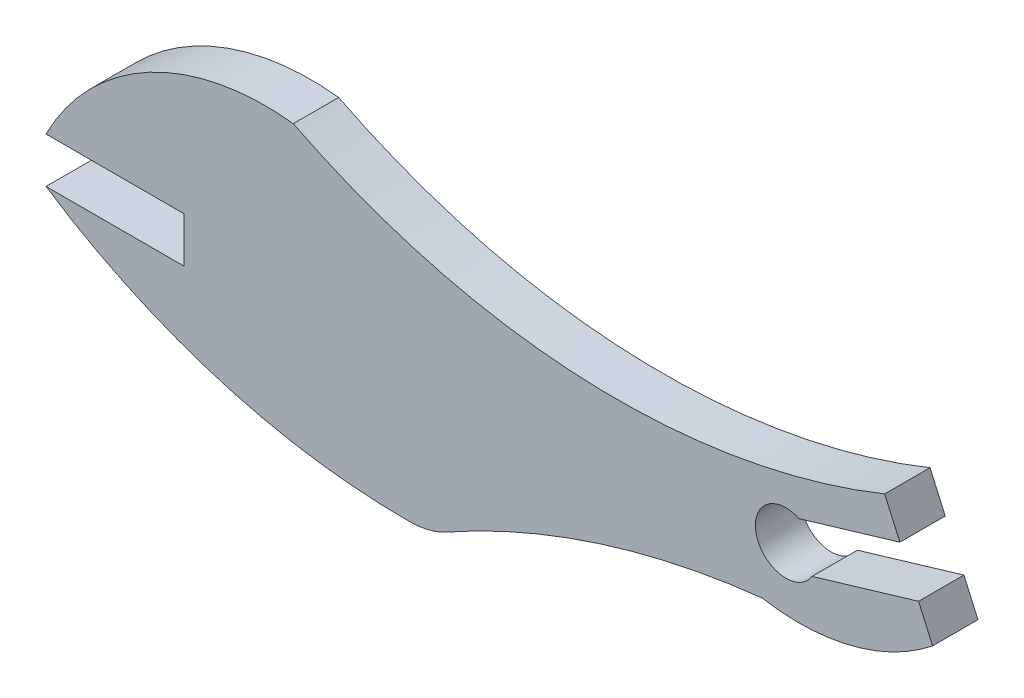
SolidWorks part; units mm, degrees
ref_plane "Front Plane" through (0, 0, 0) normal (0, 0, 1) x (1, 0, 0)
ref_plane "Top Plane" through (0, 0, 0) normal (0, 1, 0) x (1, 0, 0)
ref_plane "Right Plane" through (0, 0, 0) normal (1, 0, 0) x (0, 0, -1)
sketch "Sketch1" plane through (0, 0, 0) normal (0, 0, 1) x (1, 0, 0)
  line L0 (4.3603, 0) -> (4.3603, -1.524)
  line L1 (4.3603, -1.524) -> (-0.27, -1.524)
  line L2 (29.5018, 0) -> (29.0286, 1.062)
  line L3 (4.3603, 0) -> (-0.27, 0)
  line L4 (28.403, 2.4658) -> (27.8911, 3.6146)
  line L5 (28.403, 2.4658) -> (25.0182, 1.4583)
  line L6 (29.0286, 1.062) -> (25.453, -0.0024)
  arc A0 (-0.27, -1.524) -> (11.9642, -5.1656) centre (11.871, 16.8934) ccw
  arc A1 (13.1933, -4.8424) -> (23.7736, -1.4699) centre (26.7445, -29.0729) cw
  arc A2 (11.9642, -5.1656) -> (13.1933, -4.8424) centre (11.9534, -2.6256) ccw
  arc A3 (27.8911, 3.6146) -> (8.0338, 4.4536) centre (18.8892, 25.9668) cw
  arc A4 (-0.27, 0) -> (8.0338, 4.4536) centre (7.0928, -3.7601) cw
  arc A5 (29.5018, 0) -> (23.7736, -1.4699) centre (25.0066, 5.6214) cw
  arc A6 (25.0182, 1.4583) -> (25.453, -0.0024) centre (24.5767, 0.5318) ccw
  dimension "D1" = 2.54
extrude "Boss-Extrude1" add sketch "Sketch1" along normal blind 1.524
